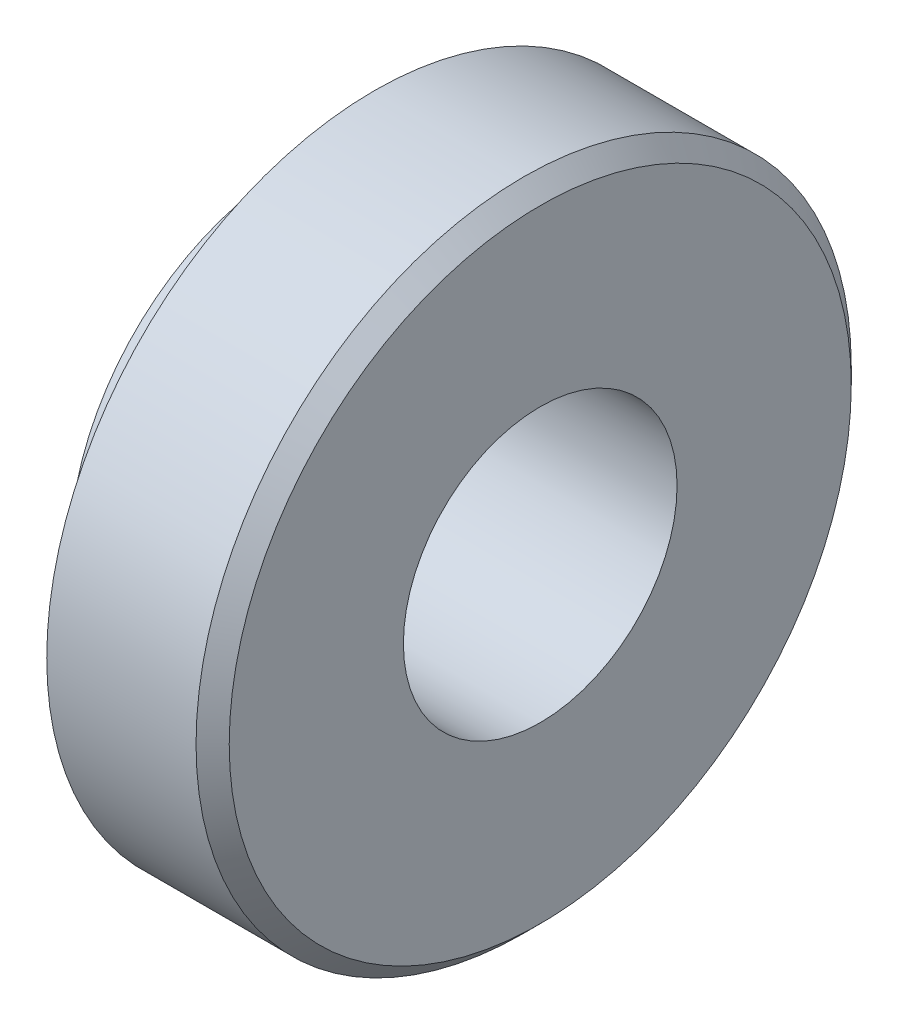
SolidWorks part; units mm, degrees
ref_plane "Plan de face" through (0, 0, 0) normal (0, 0, 1) x (1, 0, 0)
ref_plane "Plan de dessus" through (0, 0, 0) normal (0, 1, 0) x (1, 0, 0)
ref_plane "Plan de droite" through (0, 0, 0) normal (1, 0, 0) x (0, 0, -1)
sketch "Esquisse1" plane through (0, 0, 0) normal (0, 0, 1) x (1, 0, 0)
  line L0 (0, 0) -> (-2.98, 0)
  line L1 (-2.98, 0) -> (-2.98, 2.69)
  line L2 (-2.98, 2.69) -> (-2, 2.69)
  line L3 (-2, 2.69) -> (-2, 3.95)
  line L4 (-2, 3.95) -> (0, 3.95)
  line L5 (0, 3.95) -> (0, 0)
  line L6 (0, 0) -> (10.6574, 0) construction
  dimension "D1" = 2
  dimension "D2" = 7.9
  dimension "D3" = 0.98
  dimension "D4" = 5.38
revolve "Révolution1" add sketch "Esquisse1" angle 360 about L6
hole_wizard "Trou taraudé M4x0.71" positions "Esquisse3D1" profile "Esquisse2" tap size "M4x0.7" standard "ISO" end condition through all
sketch3d "Esquisse3D1"
  circle A0 centre (-2.98, 0, 0) radius 2.69 construction
  point P0 (-2.98, 0, 0)
  point P6 (-5.67, 0, 0)
sketch "Esquisse2" plane through (-2.98, 0, 0) normal (0, 1, 0) x (0, 0, 1)
  line L0 (0, 0) -> (0, 2.98)
  line L1 (0, 2.98) -> (1.65, 2.98)
  line L2 (1.65, 2.98) -> (1.65, 0)
  line L5 (1.65, 0) -> (0, 0)
  line L11 (0, -6.35) -> (0, 107.95) construction
  dimension "Diamètre du trou pour taraudage jusqu'au prochain" = 3.3
  dimension "Profondeur du trou pour taraudage jusqu'au prochain" = 2.98
cosmetic thread "Filetage de perçage1" parameters "D2"=4
chamfer "Chanfrein1" distance 0.2 angle 45 1 edges at (0, 0, 3.95)
